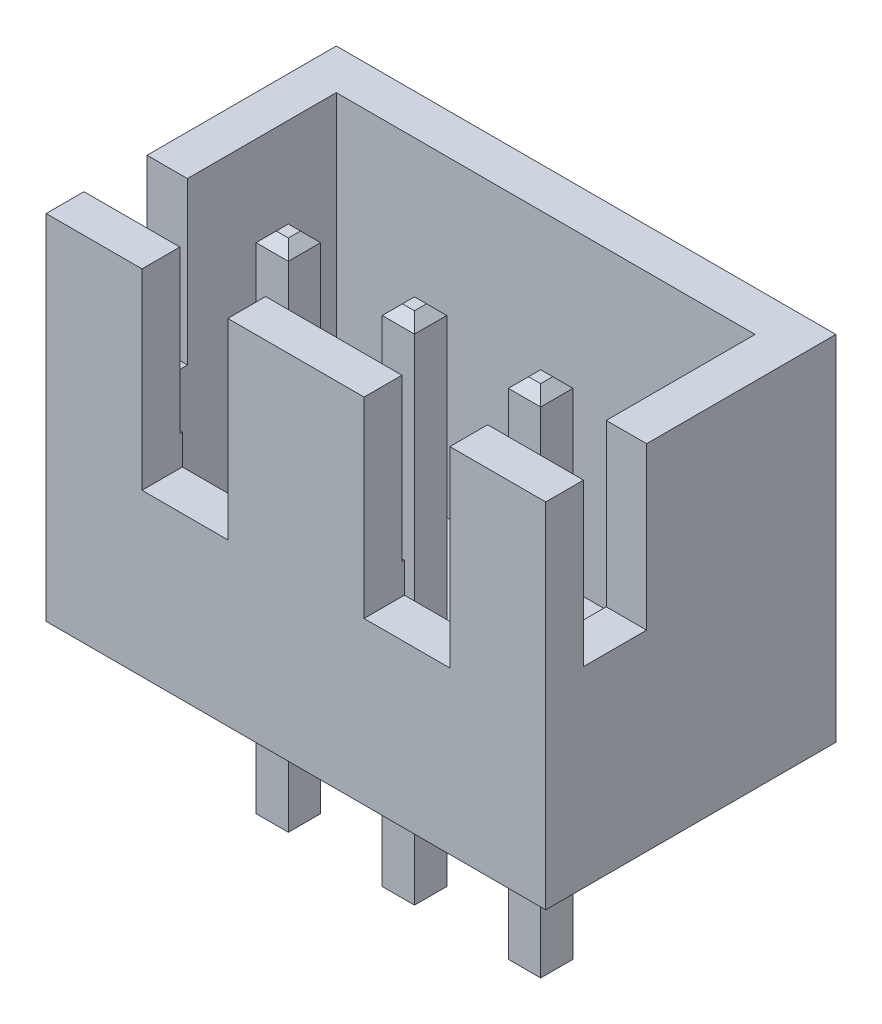
SolidWorks part; units mm, degrees
other "Camera1"
ref_plane "Front Plane" through (0, 0, 0) normal (0, 0, 1) x (1, 0, 0)
ref_plane "Top Plane" through (0, 0, 0) normal (0, 1, 0) x (1, 0, 0)
ref_plane "Right Plane" through (0, 0, 0) normal (1, 0, 0) x (0, 0, -1)
sketch "Sketch1" plane through (0, 0, 0) normal (0, 1, 0) x (1, 0, 0)
  line L1 (-4.95, 2.875) -> (4.95, 2.875)
  line L2 (-4.95, 2.875) -> (-4.95, -2.875)
  line L3 (-4.95, -2.875) -> (4.95, -2.875)
  line L4 (4.95, 2.875) -> (4.95, -2.875)
  line L5 (-4.95, 2.875) -> (4.95, -2.875) construction
  line L6 (-4.95, -2.875) -> (4.95, 2.875) construction
  point P0 (0, 0)
  dimension "D1" = 5.75
  dimension "D2" = 9.9
extrude "Boss-Extrude1" add sketch "Sketch1" along normal blind 7
shell "Shell1" thickness 0.8
sketch "Sketch2" plane through (4.95, 0, 0) normal (1, 0, 0) x (0, 0, -1)
  line L0 (-0.875, 7) -> (-0.875, 3.8)
  line L1 (-2.875, 7) -> (2.875, 7) construction
  line L2 (-2.125, 3.8) -> (-2.125, 7)
  line L3 (-2.125, 7) -> (-0.875, 7)
  line L4 (-2.875, 7) -> (-2.875, 0) construction
  line L5 (-0.875, 3.8) -> (-2.125, 3.8)
  dimension "D1" = 0.75
  dimension "D2" = 1.25
  dimension "D3" = 3.2
extrude "Cut-Extrude1" cut sketch "Sketch2" against normal through all
sketch "Sketch3" plane through (0, 0, 2.875) normal (0, 0, 1) x (1, 0, 0)
  line L0 (-3.05, 7) -> (-3.05, 3.2)
  line L1 (-4.95, 7) -> (4.95, 7) construction
  line L2 (-4.95, 7) -> (-4.95, 0) construction
  line L3 (-1.35, 3.2) -> (-3.05, 3.2)
  line L4 (3.05, 3.2) -> (1.35, 3.2)
  line L5 (-1.35, 3.2) -> (-1.35, 7)
  line L6 (-1.35, 7) -> (-3.05, 7)
  line L8 (0, 7) -> (0, 0) construction
  line L9 (1.35, 7) -> (3.05, 7)
  line L10 (1.35, 3.2) -> (1.35, 7)
  line L14 (3.05, 7) -> (3.05, 3.2)
  dimension "D1" = 1.9
  dimension "D2" = 1.7
  dimension "D3" = 3.8
extrude "Cut-Extrude2" cut sketch "Sketch3" against normal up to next
sketch "Sketch4" plane through (0, 0, 0) normal (0, -1, 0) x (1, 0, 0)
  line L1 (-2.82, 0.845) -> (-2.18, 0.845)
  line L2 (-2.82, 0.845) -> (-2.82, 0.205)
  line L3 (-2.82, 0.205) -> (-2.18, 0.205)
  line L4 (-2.18, 0.845) -> (-2.18, 0.205)
  line L5 (-2.82, 0.845) -> (-2.18, 0.205) construction
  line L6 (-2.82, 0.205) -> (-2.18, 0.845) construction
  line L7 (0, 1.9141) -> (0, 0) construction
  line L8 (0, 0) -> (2.4975, 0) construction
  line L9 (-4.95, 2.875) -> (4.95, 2.875) construction
  line L10 (-0.32, 0.845) -> (0.32, 0.845)
  line L11 (-0.32, 0.845) -> (-0.32, 0.205)
  line L12 (-0.32, 0.205) -> (0.32, 0.205)
  line L13 (0.32, 0.845) -> (0.32, 0.205)
  line L14 (2.18, 0.845) -> (2.82, 0.845)
  line L15 (2.18, 0.845) -> (2.18, 0.205)
  line L16 (2.18, 0.205) -> (2.82, 0.205)
  line L17 (2.82, 0.845) -> (2.82, 0.205)
  point P0 (-2.5, 0.525)
  dimension "D1" = 0.64
  dimension "D2" = 0.64
  dimension "D4" = 2.35
  dimension "D6" = 2.5
  dimension "D5" = 3
extrude "Boss-Extrude2" add sketch "Sketch4" along normal blind 3.45 and the other way blind 6.75
chamfer "Chamfer1" distance 0.2 angle 45 24 edges at (-2.5, -3.45, 0.205) (-2.82, -3.45, 0.525) (-2.5, -3.45, 0.845) (-2.18, -3.45, 0.525) (-2.5, 6.75, 0.845) (-2.82, 6.75, 0.525) (-2.5, 6.75, 0.205) (-2.18, 6.75, 0.525) (2.5, -3.45, 0.205) (2.18, -3.45, 0.525) (2.5, -3.45, 0.845) (2.82, -3.45, 0.525) (0, -3.45, 0.205) (-0.32, -3.45, 0.525) (0, -3.45, 0.845) (0.32, -3.45, 0.525) (2.5, 6.75, 0.845) (2.18, 6.75, 0.525) (2.5, 6.75, 0.205) (2.82, 6.75, 0.525) (0, 6.75, 0.845) (-0.32, 6.75, 0.525) (0, 6.75, 0.205) (0.32, 6.75, 0.525)
